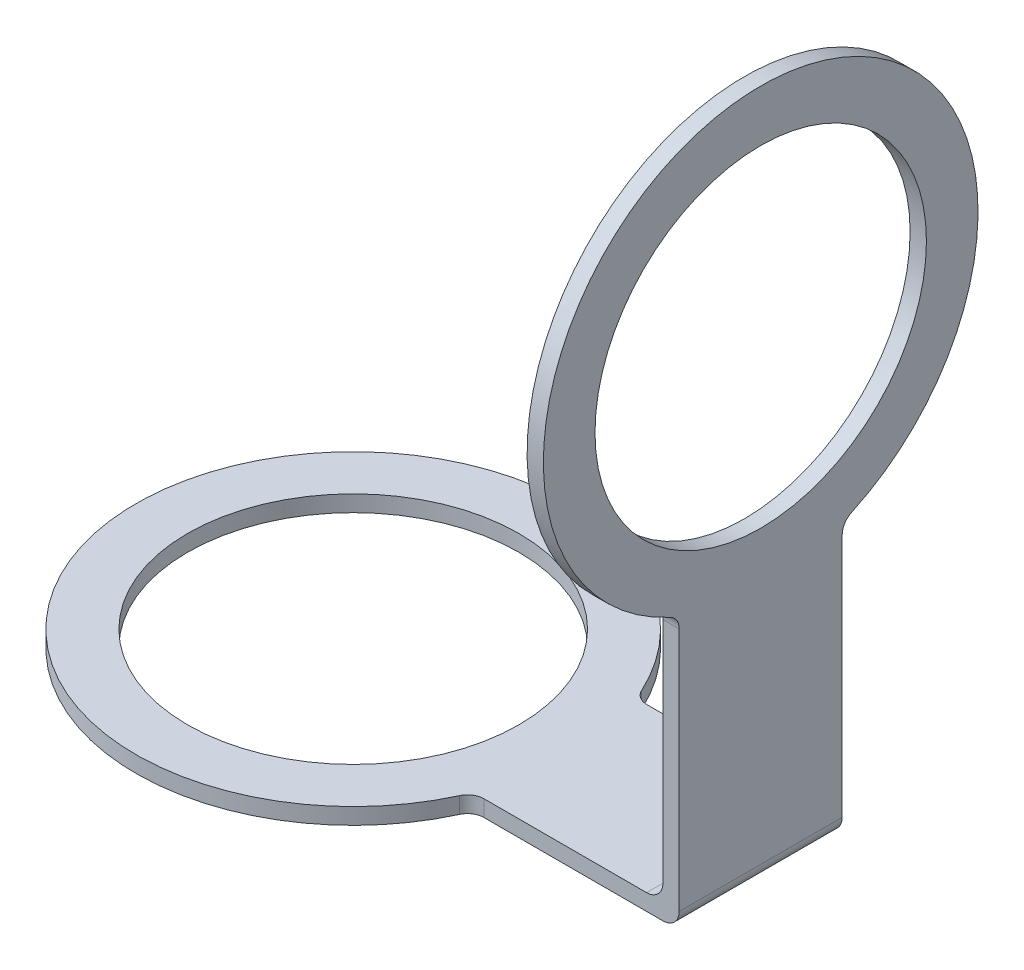
SolidWorks part; units mm, degrees
ref_plane "Front Plane" through (0, 0, 0) normal (0, 0, 1) x (1, 0, 0)
ref_plane "Top Plane" through (0, 0, 0) normal (0, 1, 0) x (1, 0, 0)
ref_plane "Right Plane" through (0, 0, 0) normal (1, 0, 0) x (0, 0, -1)
sketch "Sketch1" plane through (0, 0, 0) normal (0, 1, 0) x (1, 0, 0)
  circle A0 centre (0, 0) radius 40
  circle A1 centre (0, 0) radius 30.5
  dimension "D1" = 80
  dimension "D2" = 61
extrude "Boss-Extrude1" add sketch "Sketch1" along normal blind 3
sketch "Sketch2" plane through (0, 3, 0) normal (0, 1, 0) x (1, 0, 0)
  line L1 (35, 15) -> (75, 15)
  line L2 (35, 15) -> (35, -15)
  line L3 (35, -15) -> (75, -15)
  line L4 (75, 15) -> (75, -15)
  circle A0 centre (0, 0) radius 30.5 construction
  dimension "D1" = 30
  dimension "D2" = 15
  dimension "D3" = 35
  dimension "D4" = 40
extrude "Boss-Extrude2" add sketch "Sketch2" against normal up to surface (3 mm away) up to face at (0, 0, 40)
sketch "Sketch3" plane through (75, 0, 0) normal (1, 0, 0) x (0, 0, -1)
  line L0 (15, 0) -> (15, 3) construction
  line L1 (-15, 0) -> (15, 0)
  line L2 (-15, 0) -> (-15, 50)
  line L4 (15, 0) -> (15, 50)
  arc A0 (15, 50) -> (-15, 50) centre (0, 87.081) ccw
  circle A1 centre (0, 87.081) radius 30.5
  dimension "D1" = 80
  dimension "D2" = 61
  dimension "D3" = 50
extrude "Boss-Extrude3" add sketch "Sketch3" against normal blind 3
fillet "Fillet1" radius 3 4 edges at (37.081, 1.5, 15) (37.081, 1.5, -15) (73.5, 50, 15) (73.5, 50, -15)
fillet "Fillet2" radius 3 2 edges at (72, 3, 0) (75, 0, 0)
